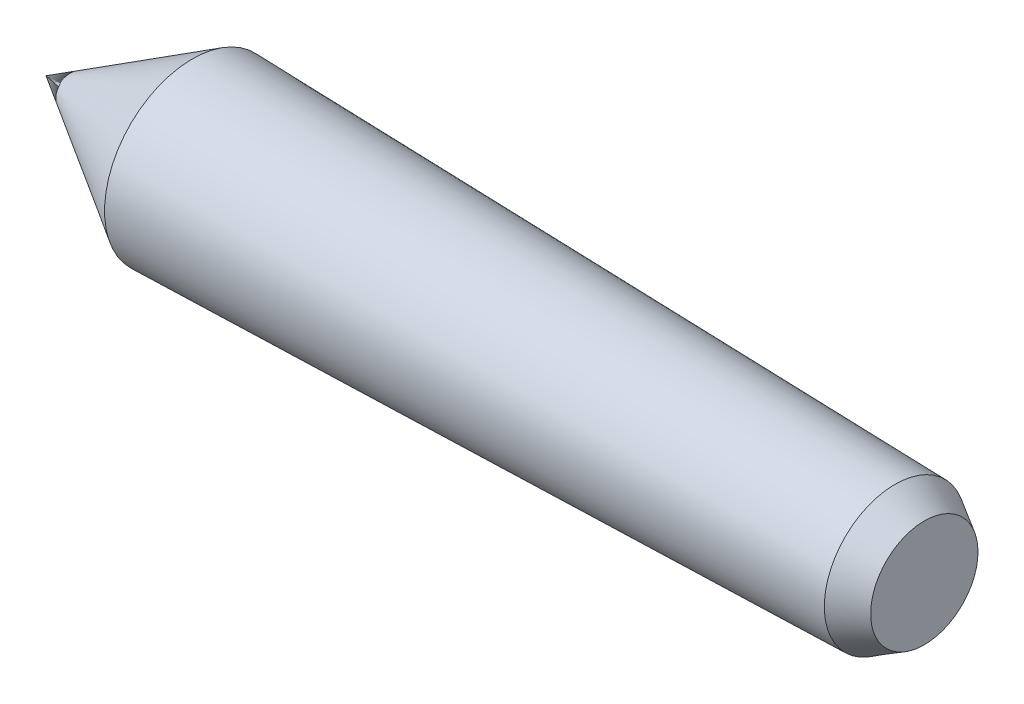
SolidWorks part; units mm, degrees
ref_plane "Front Plane" through (0, 0, 0) normal (0, 0, 1) x (1, 0, 0)
ref_plane "Top Plane" through (0, 0, 0) normal (0, 1, 0) x (1, 0, 0)
ref_plane "Right Plane" through (0, 0, 0) normal (1, 0, 0) x (0, 0, -1)
sketch "Sketch1" plane through (0, 0, 0) normal (0, 0, 1) x (1, 0, 0)
  line L0 (0, 0) -> (15, 9)
  line L1 (15, 9) -> (87, 7.25)
  line L2 (87, 7.25) -> (90, 5.5)
  line L3 (90, 5.5) -> (90, 0)
  line L4 (90, 0) -> (0, 0)
  dimension "D1" = 90
  dimension "D2" = 15
  dimension "D3" = 9
  dimension "D4" = 5.5
  dimension "D5" = 7.25
  dimension "D6" = 3
revolve "Revolve1" add sketch "Sketch1" angle 360 about L4
